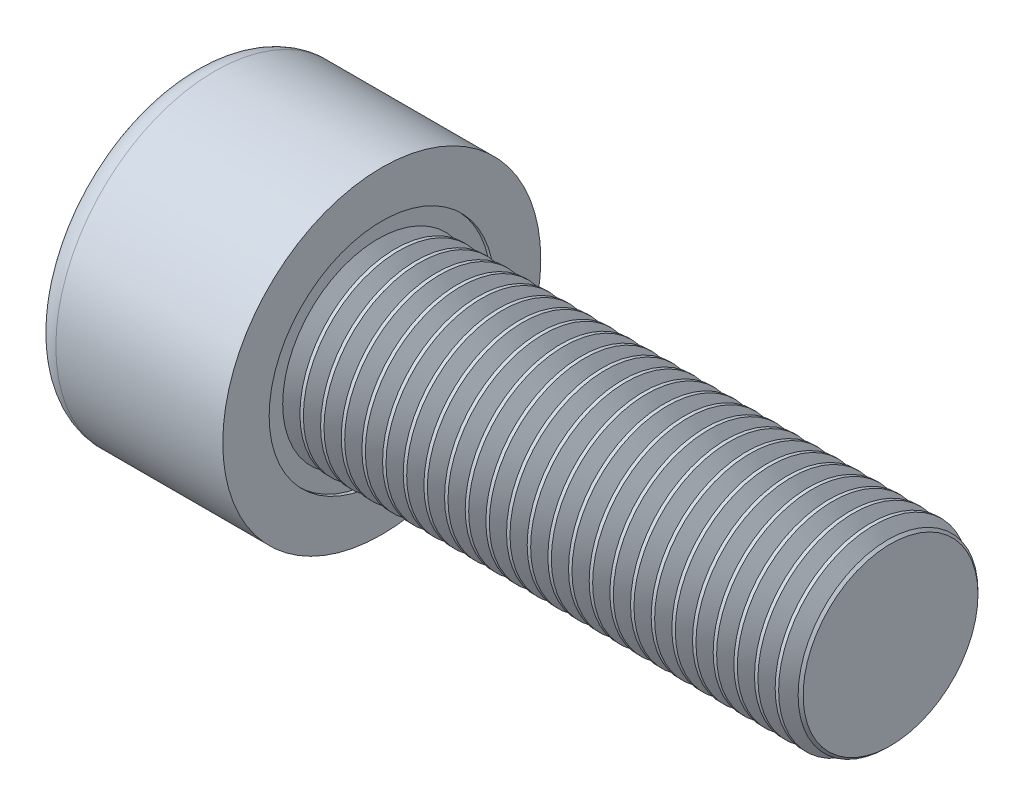
SolidWorks part; units mm, degrees
ref_plane "Front" through (0, 0, 0) normal (0, 0, 1) x (1, 0, 0)
ref_plane "Top" through (0, 0, 0) normal (0, 1, 0) x (1, 0, 0)
ref_plane "Right" through (0, 0, 0) normal (1, 0, 0) x (0, 0, -1)
sketch "Sketch1" plane through (0, 0, 0) normal (1, 0, 0) x (0, 0, -1)
  circle A0 centre (0, 0) radius 5
  dimension "dk" = 10
extrude "BaseHead" add sketch "Sketch1" along normal blind 6
sketch "Sketch2" plane through (6, 0, 0) normal (1, 0, 0) x (0, 0, -1)
  circle A0 centre (0, 0) radius 3
  dimension "d" = 6
extrude "BaseBody" add sketch "Sketch2" along normal blind 16
cosmetic thread "ThreadCosmetic1" [suppressed] parameters "b"=16, "D2"=4.917
sketch "Sketch3" plane through (0, 0, 0) normal (1, 0, 0) x (0, 0, -1)
  line L1 (2.8868, 0) -> (1.4434, 2.5)
  line L2 (1.4434, 2.5) -> (-1.4434, 2.5)
  line L3 (-1.4434, 2.5) -> (-2.8868, 0)
  line L4 (-2.8868, 0) -> (-1.4434, -2.5)
  line L5 (-1.4434, -2.5) -> (1.4434, -2.5)
  line L6 (1.4434, -2.5) -> (2.8868, 0)
  circle A0 centre (0, 0) radius 2.5 construction
  dimension "s" = 5
  dimension "e" = 5.7735
extrude "HexagonSocket" cut sketch "Sketch3" along normal blind 3
sketch "Sketch4" plane through (-4.1961, 0.75, 0) normal (0, 0, 1) x (-1, 0, 0)
  line L0 (-7.1961, 3.25) -> (-8.6395, 0.75)
  line L2 (-8.6395, 0.75) -> (-7.1961, 0.75)
  line L3 (-7.1961, 0.75) -> (-7.1961, 3.25)
  line L4 (-5.0351, 0.75) -> (0.839, 0.75) construction
  line L5 (-26.1961, 0.75) -> (-10.1961, 0.75) construction
  line L6 (-10.1961, 0.75) -> (-4.1961, 0.75) construction
  dimension "m" = 60
revolve "Cut-Revolve1" cut sketch "Sketch4" angle 360 about L4
fillet "HeadFillet" [suppressed] radius 0.25
fillet "TopFillet" radius 0.75 1 edges at (0, 0, -5)
chamfer "Chamfer1" distance 0.25 angle 45 1 edges at (22, 0, -3)
sketch "Sketch5" plane through (0, 0, 0) normal (0, 0, 1) x (1, 0, 0)
  line L0 (21.75, 2.531) -> (22.0207, 3)
  line L1 (22.0207, 3) -> (22.0207, 3.5415)
  line L2 (22.0207, 3.5415) -> (21.4792, 3.5415)
  line L3 (21.4792, 3.5415) -> (21.4792, 3)
  line L4 (21.4792, 3) -> (21.75, 2.531)
  line L5 (0, 0) -> (7.8886, 0) construction
  line L6 (21.75, -3) -> (21.75, 3) construction
  dimension "D1" = 6
  dimension "D2" = 0.5415
revolve "Cut-Revolve10" cut sketch "Sketch5" angle 360 about L5
pattern_linear "LPattern10" count 25 spacing 0.6498 along (-1, 0, 0) of "Cut-Revolve10"
equation "\"r1@TopFillet\" = \"d@Sketch2\" / 8"
equation "\"D1@Chamfer1\" = \"r@HeadFillet\""
equation "\"D1@Sketch5\" = \"d@Sketch2\""
equation "\"D2@Sketch5\" =  ( \"d@Sketch2\" - \"D2@ThreadCosmetic1\" )  / 2"
equation "\"D3@LPattern10\" = \"D2@Sketch5\" * 1.2"
equation "\"D1@LPattern10\" = \"b@ThreadCosmetic1\" / \"D3@LPattern10\""
